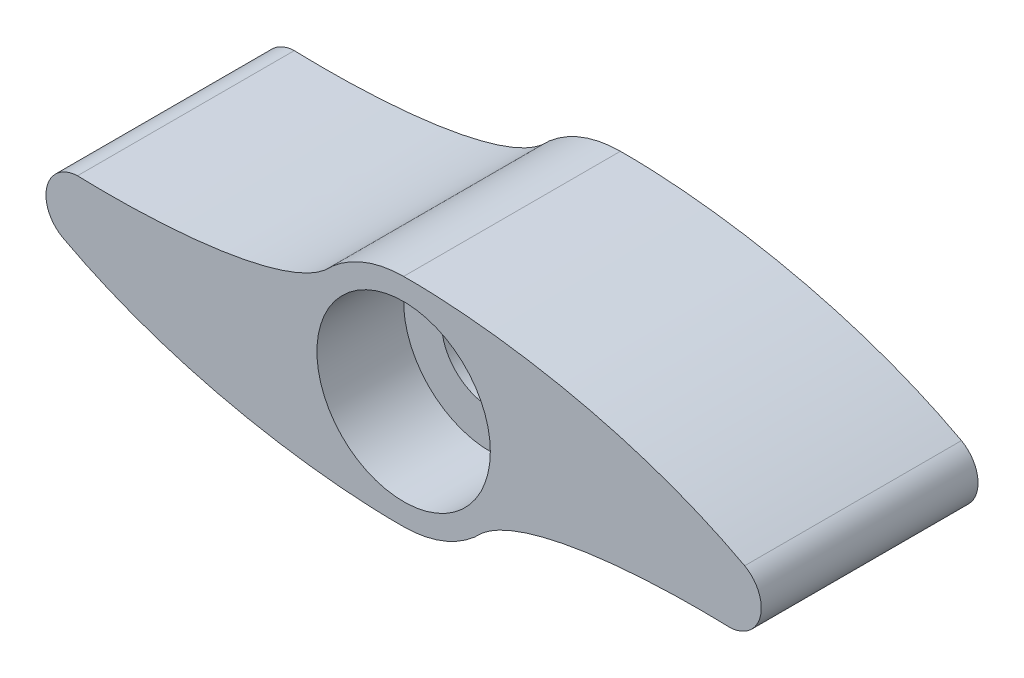
SolidWorks part; units mm, degrees
ref_plane "Спереди" through (0, 0, 0) normal (0, 0, 1) x (1, 0, 0)
ref_plane "Сверху" through (0, 0, 0) normal (0, 1, 0) x (1, 0, 0)
ref_plane "Справа" through (0, 0, 0) normal (1, 0, 0) x (0, 0, -1)
sketch "Эскиз1" plane through (0, 0, 0) normal (0, 0, 1) x (1, 0, 0)
  line L0 (21.7984, 0) -> (-21.4718, 0) construction
  line L1 (0, 6.017) -> (0, -13.5956) construction
  arc A0 (0, -5) -> (3.6325, -3.4358) centre (0, 0) ccw
  arc A1 (-15.0441, 1.4994) -> (-15.7344, -1.3079) centre (-15, 0) ccw
  arc A2 (0, 5) -> (-3.6325, 3.4358) centre (0, 0) ccw
  arc A3 (15.0441, -1.4994) -> (15.7344, 1.3079) centre (15, 0) ccw
  spline S0 degree 3 poles (-15.7344, -1.3079) (-10.0868, -4.3397) (-3.2849, -5.0362) (0, -5) knots 0 0 0 0 1 1 1 1
  spline S1 degree 3 poles (-15.0441, 1.4994) (-10.3946, 1.3554) (-5.4593, 1.9021) (-3.6325, 3.4358) knots 0 0 0 0 1 1 1 1
  spline S4 degree 3 poles (15.0441, -1.4994) (10.3946, -1.3554) (5.4593, -1.9021) (3.6325, -3.4358) knots 0 0 0 0 1 1 1 1
  spline S5 degree 3 poles (15.7344, 1.3079) (10.0868, 4.3397) (3.2849, 5.0362) (0, 5) knots 0 0 0 0 1 1 1 1
  dimension "D1" = 10
  dimension "D2" = 3
  dimension "D4" = 15
extrude "Бобышка-Вытянуть1" add sketch "Эскиз1" along normal blind 10
hole_wizard "Цековка для винта с внутренним шестигранником M41" positions "Эскиз4" profile "Эскиз3" counterbore size "M4" standard "Ansi Metric" end condition through all
sketch "Эскиз4" plane through (0, 0, 10) normal (0, 0, 1) x (1, 0, 0)
  point P0 (0, 0)
sketch "Эскиз3" plane through (0, 0, 10) normal (1, 0, 0) x (0, -1, 0)
  line L0 (0, 0) -> (0, 10)
  line L1 (0, 10) -> (2.25, 10)
  line L3 (2.25, 10) -> (2.25, 4)
  line L4 (2.25, 4) -> (4, 4)
  line L5 (4, 4) -> (4, 0)
  line L7 (4, 0) -> (0, 0)
  line L11 (0, -6.35) -> (0, 107.95) construction
  dimension "Диаметр сквозного отверстия" = 4.5
  dimension "Глубина сквозного отверстия" = 10
  dimension "Диаметр цековки" = 8
  dimension "Глубина цековки" = 4
